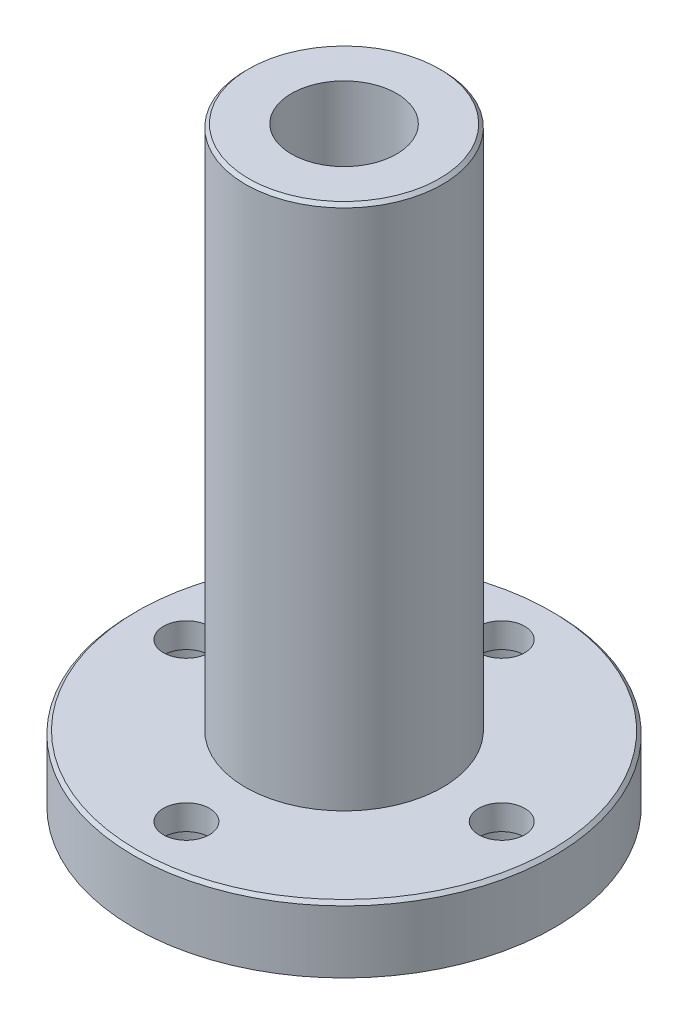
SolidWorks part; units mm, degrees
material "AISI 304"
ref_plane "Front Plane" through (0, 0, 0) normal (0, 0, 1) x (1, 0, 0)
ref_plane "Top Plane" through (0, 0, 0) normal (0, 1, 0) x (1, 0, 0)
ref_plane "Right Plane" through (0, 0, 0) normal (1, 0, 0) x (0, 0, -1)
sketch "Sketch1" plane through (0, 0, 0) normal (0, 1, 0) x (1, 0, 0)
  circle A0 centre (0, 0) radius 16
  dimension "D1" = 32
extrude "Boss-Extrude3" add sketch "Sketch1" along normal blind 5
sketch "Sketch4" plane through (0, 5, 0) normal (0, 1, 0) x (1, 0, 0)
  circle A0 centre (0, 0) radius 7.5
  dimension "D1" = 15
extrude "Boss-Extrude4" add sketch "Sketch4" along normal blind 40
sketch "Sketch5" plane through (0, 5, 0) normal (0, 1, 0) x (1, 0, 0)
  circle A0 centre (0, 0) radius 12 construction
  circle A1 centre (0, 12) radius 1.75
  circle A2 centre (-12, 0) radius 1.75
  circle A3 centre (12, 0) radius 1.75
  circle A4 centre (0, -12) radius 1.75
  dimension "D1" = 24
  dimension "D2" = 3.5
  dimension "D3" = 3.5
  dimension "D4" = 3.5
  dimension "D5" = 3.5
extrude "Cut-Extrude2" cut sketch "Sketch5" against normal blind 5
sketch "Sketch6" plane through (0, 45, 0) normal (0, 1, 0) x (1, 0, 0)
  circle A0 centre (0, 0) radius 4
  dimension "D1" = 8
extrude "Cut-Extrude3" cut sketch "Sketch6" against normal up to surface (45 mm away) up to face at (-12, 0, 1.75)
sketch "Sketch7" plane through (0, 0, 0) normal (0, -1, 0) x (1, 0, 0)
  circle A0 centre (0, 12) radius 3
  circle A1 centre (-12, 0) radius 3
  circle A2 centre (0, -12) radius 3
  circle A3 centre (12, 0) radius 3
  dimension "D1" = 6
  dimension "D2" = 6
  dimension "D3" = 6
  dimension "D4" = 6
extrude "Cut-Extrude4" cut sketch "Sketch7" against normal blind 3.1
chamfer "Chamfer1" distance 0.25 angle 45 2 edges at (0, 45, 7.5) (0, 5, 16)
